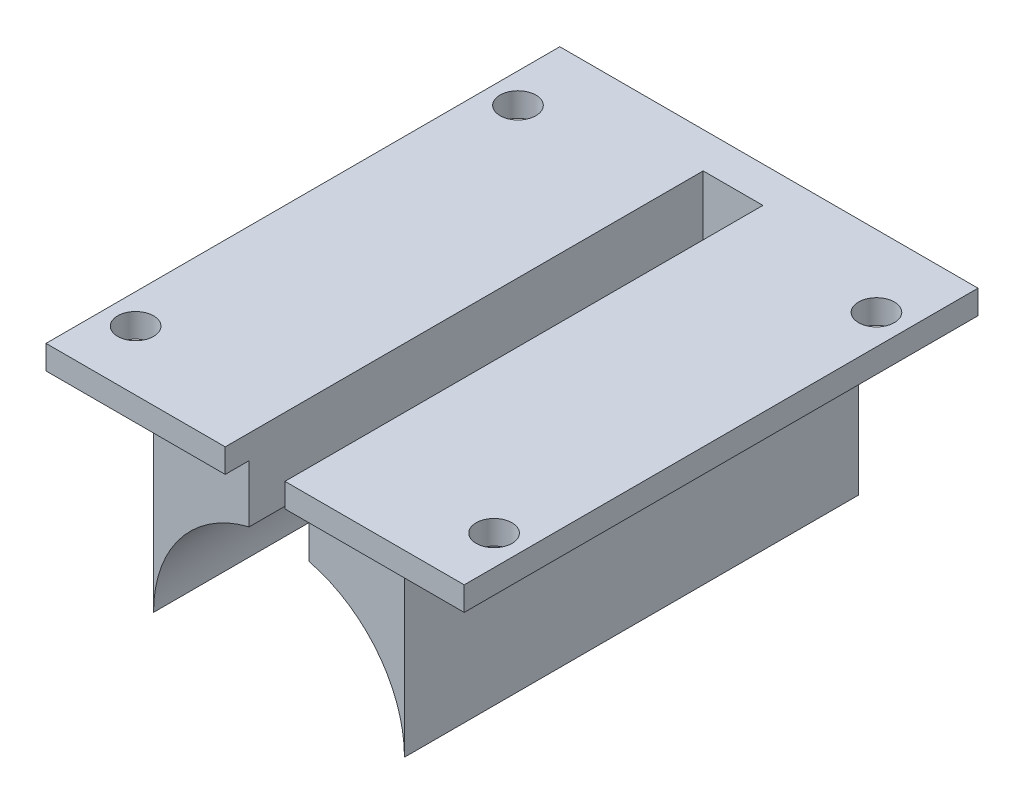
SolidWorks part; units mm, degrees
ref_plane "Alzado" through (0, 0, 0) normal (0, 0, 1) x (1, 0, 0)
ref_plane "Planta" through (0, 0, 0) normal (0, 1, 0) x (1, 0, 0)
ref_plane "Vista lateral" through (0, 0, 0) normal (1, 0, 0) x (0, 0, -1)
sketch "Croquis1" plane through (0, 0, 0) normal (0, 0, 1) x (1, 0, 0)
  line L0 (10.5, 0) -> (10.5, 10.5)
  line L2 (-10.5, 0) -> (-10.5, 10.5)
  line L6 (2.5, 17) -> (2.5, 10.198)
  line L7 (-2.5, 17) -> (-2.5, 10.198)
  line L8 (10.5, 10.5) -> (10.5, 17)
  line L9 (10.5, 17) -> (2.5, 17)
  line L11 (-10.5, 17) -> (-10.5, 10.5)
  line L12 (-2.5, 17) -> (-10.5, 17)
  arc A0 (10.5, 0) -> (2.5, 10.198) centre (0, 0) ccw
  arc A1 (-2.5, 10.198) -> (-10.5, 0) centre (0, 0) ccw
  dimension "D1" = 21
extrude "Saliente-Extruir1" add sketch "Croquis1" along normal blind 38
sketch "Croquis2" plane through (0, 17, 0) normal (0, 1, 0) x (1, 0, 0)
  line L0 (2.5, 0) -> (-2.5, 0)
  line L4 (-17.5, 2) -> (-17.5, 3)
  line L6 (-2.5, 0) -> (-2.5, -40)
  line L7 (-17.5, 3) -> (17.5, 3)
  line L9 (12.5, -40) -> (2.5, -40)
  line L11 (2.5, 0) -> (2.5, -40)
  line L13 (-2.5, -40) -> (-12.5, -40)
  line L14 (17.5, 2) -> (17.5, -40)
  line L15 (17.5, -40) -> (12.5, -40)
  line L16 (-12.5, -40) -> (-17.5, -40)
  line L17 (-17.5, -40) -> (-17.5, 2)
  line L19 (17.5, 3) -> (17.5, 2)
  circle A0 centre (-15, -3) radius 1.5
  circle A4 centre (15, -3) radius 1.5
  circle A5 centre (15, -35) radius 1.5
  circle A6 centre (-15, -35) radius 1.5
  dimension "D3" = 3
  dimension "D1" = 35
  dimension "D2" = 42
  dimension "D6" = 2
  dimension "D9" = 1
  dimension "D7" = 2
extrude "Saliente-Extruir2" add sketch "Croquis2" against normal blind 2
sketch "Croquis3" plane through (0, 17, 0) normal (0, 1, 0) x (1, 0, 0)
  line L0 (0, 3) -> (-4, 3)
  line L1 (17.5, 3) -> (-17.5, 3) construction
  line L2 (-4, 3) -> (-4, 0)
  line L3 (10.5, 0) -> (2.5, 0) construction
  line L4 (-4, 0) -> (3.997, 0)
  line L5 (-2.5, 0) -> (-10.5, 0) construction
  line L6 (3.997, 0) -> (3.997, 3)
  line L7 (3.997, 3) -> (0, 3)
  dimension "D1" = 4
  dimension "D2" = 7.997
sketch "Croquis4" plane through (0, 0, -3) normal (0, 0, -1) x (-1, 0, 0)
  circle A0 centre (0, 0) radius 4
  dimension "D1" = 8
extrude "Saliente-Extruir4" add sketch "Croquis3" against normal blind 17
extrude "Cortar-Extruir2" cut sketch "Croquis4" against normal blind 17
